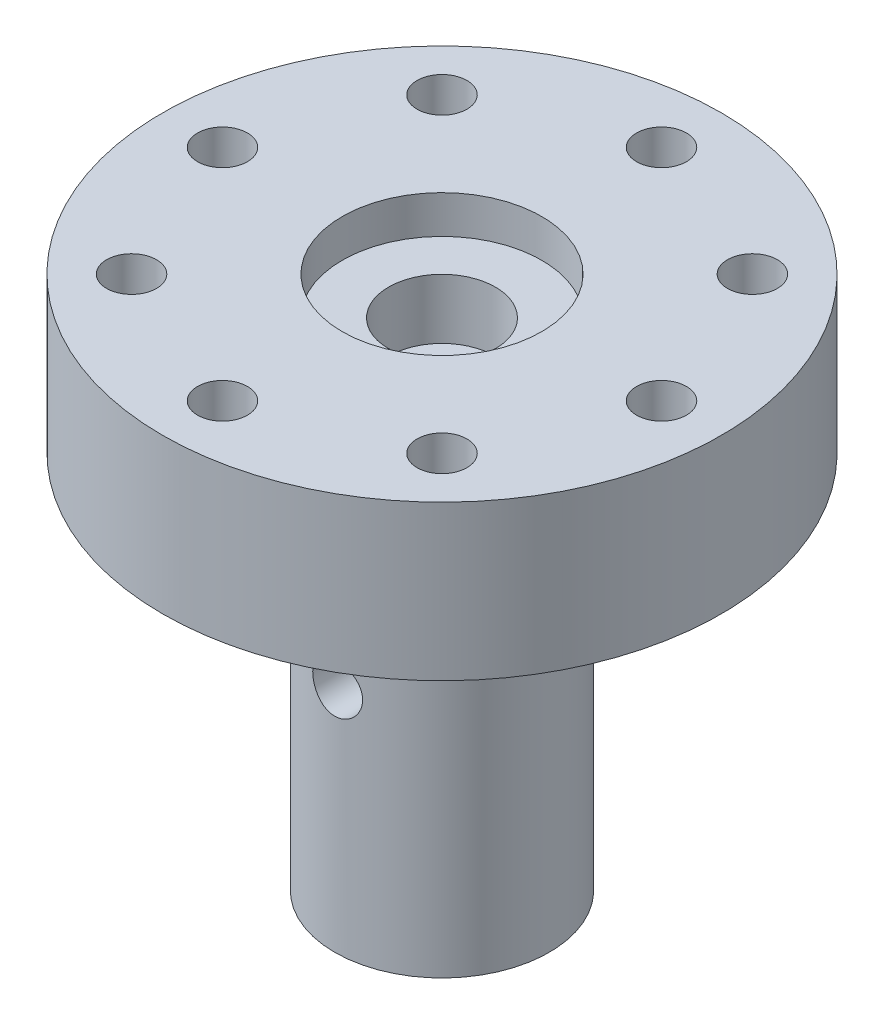
SolidWorks part; units mm, degrees
ref_plane "Front Plane" through (0, 0, 0) normal (0, 0, 1) x (1, 0, 0)
ref_plane "Top Plane" through (0, 0, 0) normal (0, 1, 0) x (1, 0, 0)
ref_plane "Right Plane" through (0, 0, 0) normal (1, 0, 0) x (0, 0, -1)
sketch "Sketch1" plane through (0, 0, 0) normal (0, 1, 0) x (1, 0, 0)
  circle A0 centre (0, 0) radius 14
  circle A9 centre (-7.7782, 7.7782) radius 1.25
  circle A10 centre (0, 11) radius 1.25
  circle A11 centre (7.7782, 7.7782) radius 1.25
  circle A12 centre (11, 0) radius 1.25
  circle A13 centre (7.7782, -7.7782) radius 1.25
  circle A14 centre (0, -11) radius 1.25
  circle A15 centre (-11, 0) radius 1.25
  circle A16 centre (-7.7782, -7.7782) radius 1.25
  point P20 (0, 0)
  dimension "D1" = 28
  dimension "D2" = 11
  dimension "D3" = 2.5
  dimension "D4" = 8
extrude "Boss-Extrude1" add sketch "Sketch1" along normal blind 7.75
sketch "Sketch2" plane through (0, 7.75, 0) normal (0, 1, 0) x (1, 0, 0)
  circle A0 centre (0, 0) radius 5
  dimension "D1" = 10
extrude "Cut-Extrude1" cut sketch "Sketch2" against normal blind 1.9
sketch "Sketch5" plane through (0, 5.85, 0) normal (0, 1, 0) x (1, 0, 0)
  circle A0 centre (0, 0) radius 2.675
  dimension "D1" = 5.35
extrude "Cut-Extrude3" cut sketch "Sketch5" against normal blind 3
sketch "Sketch3" plane through (0, 0, 0) normal (0, -1, 0) x (1, 0, 0)
  circle A0 centre (0, 0) radius 5.375
  dimension "D1" = 10.75
extrude "Boss-Extrude2" add sketch "Sketch3" along normal blind 19
sketch "Sketch4" plane through (0, 0, 0) normal (0, 0, 1) x (1, 0, 0)
  line L0 (-5.375, 0) -> (5.375, 0) construction
  circle A2 centre (0, -7.5) radius 1.25
  dimension "D1" = 2.5
  dimension "D2" = 7.5
extrude "Cut-Extrude4" cut sketch "Sketch4" against normal through all and the other way through all
